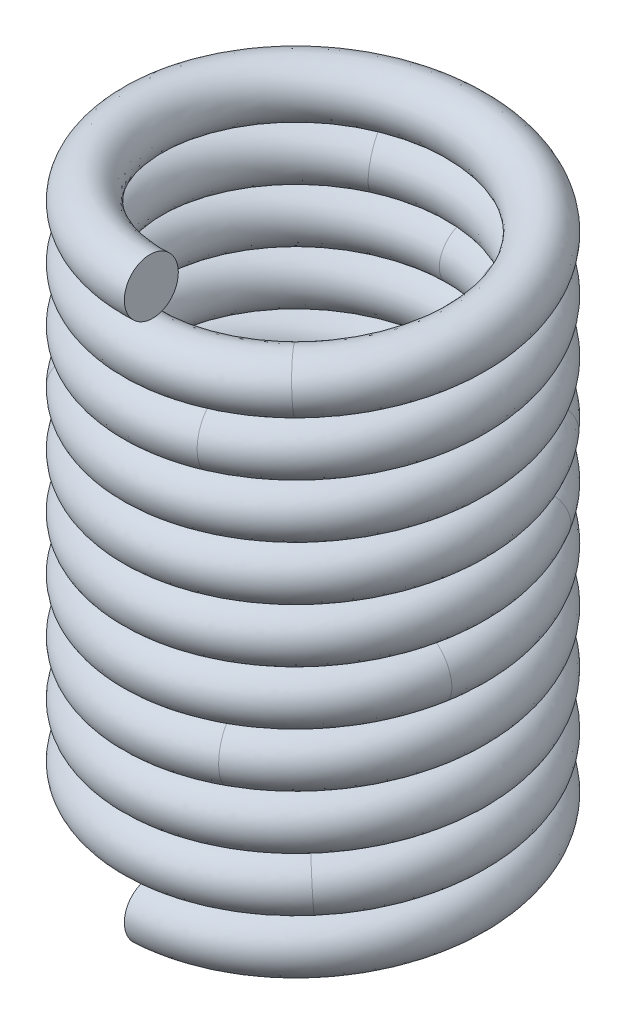
SolidWorks part; units mm, degrees
ref_plane "Front" through (0, 0, 0) normal (0, 0, 1) x (1, 0, 0)
ref_plane "Top" through (0, 0, 0) normal (0, 1, 0) x (1, 0, 0)
ref_plane "Right" through (0, 0, 0) normal (1, 0, 0) x (0, 0, -1)
sketch "Sketch1" plane through (0, 0, 0) normal (0, 1, 0) x (1, 0, 0)
  circle A0 centre (0, 0) radius 15
  dimension "D1" = 30
curve "Helix/Spiral2" pitch 5 height 50 turns 10
ref_plane "Plane2" through (0, 0, 15) normal (0.9986, 0.053, 0) x (0, 0, -1)
sketch "Sketch4" plane through (0, 0, 15) normal (0.9986, 0.053, 0) x (0, 0, -1)
  circle A0 centre (0, 0) radius 2.5
  dimension "D1" = 5
sweep "Sweep2" add profiles "Sketch4" path "Helix/Spiral2"
